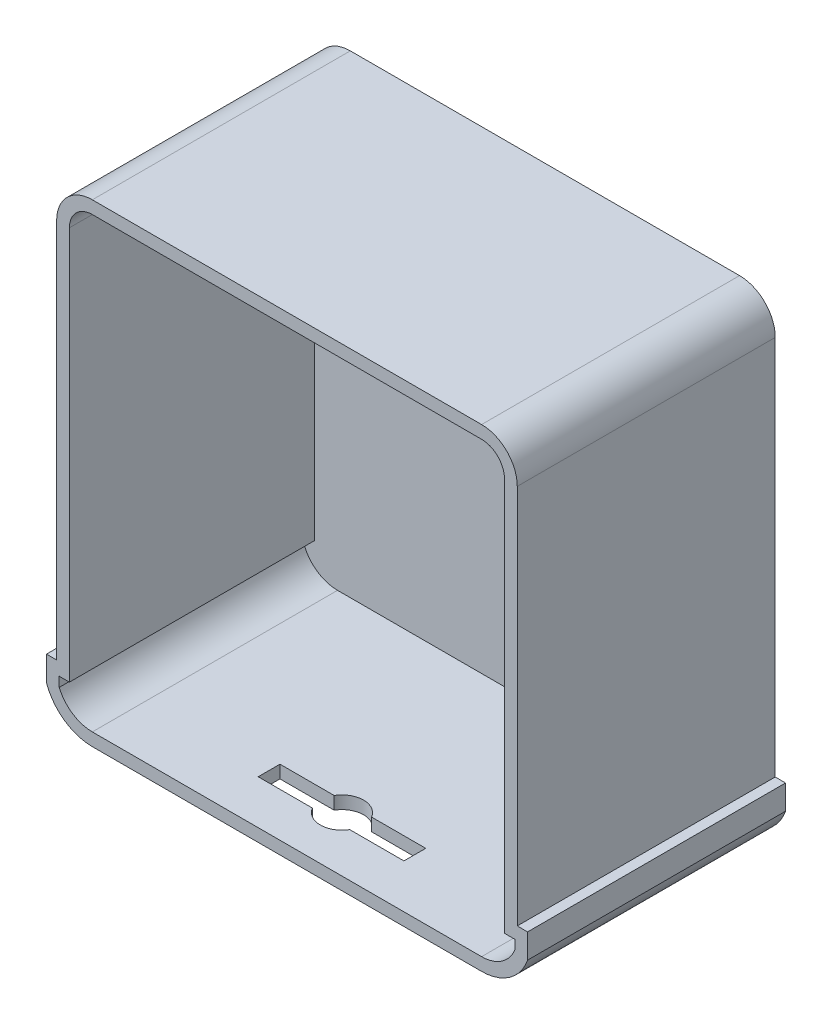
SolidWorks part; units mm, degrees
ref_plane "Front Plane" through (0, 0, 0) normal (0, 0, 1) x (1, 0, 0)
ref_plane "Top Plane" through (0, 0, 0) normal (0, 1, 0) x (1, 0, 0)
ref_plane "Right Plane" through (0, 0, 0) normal (1, 0, 0) x (0, 0, -1)
sketch "Sketch1" plane through (0, 0, 0) normal (0, 0, 1) x (1, 0, 0)
  line L8 (-325.4115, 298.1025) -> (-325.4115, 0)
  line L9 (-325.4115, 0) -> (-333.3926, 0)
  line L10 (-333.3926, 0) -> (-333.3926, -19.3975)
  line L11 (-297.4715, -44.7975) -> (7.3285, -44.7975)
  line L12 (43.3314, -19.1633) -> (43.3314, 0)
  line L13 (43.3314, 0) -> (35.2685, 0)
  line L14 (35.2685, 0) -> (35.2685, 298.1025)
  line L15 (7.3285, 326.0425) -> (-297.4715, 326.0425)
  line L16 (-325.4115, 298.1025) -> (-325.4115, 0)
  line L17 (-325.4115, 0) -> (-333.3926, 0)
  line L18 (-333.3926, 0) -> (-333.3926, -19.3975)
  line L19 (-297.4715, -44.7975) -> (7.3285, -44.7975)
  line L20 (43.3314, -19.1633) -> (43.3314, 0)
  line L21 (43.3314, 0) -> (35.2685, 0)
  line L22 (35.2685, 0) -> (35.2685, 298.1025)
  line L23 (7.3285, 326.0425) -> (-297.4715, 326.0425)
  arc A4 (-333.3926, -19.3975) -> (-297.4715, -44.7975) centre (-297.4715, -6.6975) ccw
  arc A5 (7.3285, -44.7975) -> (43.3314, -19.1633) centre (7.3285, -6.6975) ccw
  arc A6 (35.2685, 298.1025) -> (7.3285, 326.0425) centre (7.3285, 298.1025) ccw
  arc A7 (-297.4715, 326.0425) -> (-325.4115, 298.1025) centre (-297.4715, 298.1025) ccw
  arc A8 (-333.3926, -19.3975) -> (-297.4715, -44.7975) centre (-297.4715, -6.6975) ccw
  arc A9 (7.3285, -44.7975) -> (43.3314, -19.1633) centre (7.3285, -6.6975) ccw
  arc A10 (35.2685, 298.1025) -> (7.3285, 326.0425) centre (7.3285, 298.1025) ccw
  arc A11 (-297.4715, 326.0425) -> (-325.4115, 298.1025) centre (-297.4715, 298.1025) ccw
  dimension "D1" = 0
extrude "Boss-Extrude1" add sketch "Sketch1" along normal blind 10
sketch "Sketch2" plane through (0, 0, 10) normal (0, 0, 1) x (1, 0, 0)
  line L16 (-315.4115, 298.1025) -> (-315.4115, -10)
  line L17 (-315.4115, -10) -> (-323.3926, -10)
  line L18 (-323.3926, -10) -> (-323.3926, -17.547)
  line L19 (-297.4715, -34.7975) -> (7.3285, -34.7975)
  line L20 (33.3314, -17.3491) -> (33.3314, -10)
  line L21 (33.3314, -10) -> (25.2685, -10)
  line L22 (25.2685, -10) -> (25.2685, 298.1025)
  line L23 (7.3285, 316.0425) -> (-297.4715, 316.0425)
  line L24 (-315.4115, 298.1025) -> (-315.4115, -10)
  line L25 (-315.4115, -10) -> (-323.3926, -10)
  line L26 (-323.3926, -10) -> (-323.3926, -17.547)
  line L27 (-297.4715, -34.7975) -> (7.3285, -34.7975)
  line L28 (33.3314, -17.3491) -> (33.3314, -10)
  line L29 (33.3314, -10) -> (25.2685, -10)
  line L30 (25.2685, -10) -> (25.2685, 298.1025)
  line L31 (7.3285, 316.0425) -> (-297.4715, 316.0425)
  line L32 (-325.4115, 298.1025) -> (-325.4115, 0)
  line L33 (-325.4115, 0) -> (-333.3926, 0)
  line L34 (-333.3926, 0) -> (-333.3926, -19.3975)
  line L35 (-297.4715, -44.7975) -> (7.3285, -44.7975)
  line L36 (43.3314, -19.1633) -> (43.3314, 0)
  line L37 (43.3314, 0) -> (35.2685, 0)
  line L38 (35.2685, 0) -> (35.2685, 298.1025)
  line L39 (7.3285, 326.0425) -> (-297.4715, 326.0425)
  line L40 (-325.4115, 298.1025) -> (-325.4115, 0)
  line L41 (-325.4115, 0) -> (-333.3926, 0)
  line L42 (-333.3926, 0) -> (-333.3926, -19.3975)
  line L43 (-297.4715, -44.7975) -> (7.3285, -44.7975)
  line L44 (43.3314, -19.1633) -> (43.3314, 0)
  line L45 (43.3314, 0) -> (35.2685, 0)
  line L46 (35.2685, 0) -> (35.2685, 298.1025)
  line L47 (7.3285, 326.0425) -> (-297.4715, 326.0425)
  arc A8 (-297.4715, 316.0425) -> (-315.4115, 298.1025) centre (-297.4715, 298.1025) ccw
  arc A9 (-323.3926, -17.547) -> (-297.4715, -34.7975) centre (-297.4715, -6.6975) ccw
  arc A10 (7.3285, -34.7975) -> (33.3314, -17.3491) centre (7.3285, -6.6975) ccw
  arc A11 (25.2685, 298.1025) -> (7.3285, 316.0425) centre (7.3285, 298.1025) ccw
  arc A12 (-297.4715, 316.0425) -> (-315.4115, 298.1025) centre (-297.4715, 298.1025) ccw
  arc A13 (-323.3926, -17.547) -> (-297.4715, -34.7975) centre (-297.4715, -6.6975) ccw
  arc A14 (7.3285, -34.7975) -> (33.3314, -17.3491) centre (7.3285, -6.6975) ccw
  arc A15 (25.2685, 298.1025) -> (7.3285, 316.0425) centre (7.3285, 298.1025) ccw
  arc A16 (-297.4715, 326.0425) -> (-325.4115, 298.1025) centre (-297.4715, 298.1025) ccw
  arc A17 (-333.3926, -19.3975) -> (-297.4715, -44.7975) centre (-297.4715, -6.6975) ccw
  arc A18 (7.3285, -44.7975) -> (43.3314, -19.1633) centre (7.3285, -6.6975) ccw
  arc A19 (35.2685, 298.1025) -> (7.3285, 326.0425) centre (7.3285, 298.1025) ccw
  arc A20 (-297.4715, 326.0425) -> (-325.4115, 298.1025) centre (-297.4715, 298.1025) ccw
  arc A21 (-333.3926, -19.3975) -> (-297.4715, -44.7975) centre (-297.4715, -6.6975) ccw
  arc A22 (7.3285, -44.7975) -> (43.3314, -19.1633) centre (7.3285, -6.6975) ccw
  arc A23 (35.2685, 298.1025) -> (7.3285, 326.0425) centre (7.3285, 298.1025) ccw
  dimension "D1" = 10
  dimension "D2" = 0
extrude "Boss-Extrude2" add sketch "Sketch2" along normal blind 192
sketch "Sketch3" plane through (0, -44.7975, 0) normal (0, -1, 0) x (1, 0, 0)
  line L1 (-202.1393, 150.4117) -> (-88.0038, 150.4117)
  line L2 (-202.1393, 150.4117) -> (-202.1393, 167.4708)
  line L3 (-202.1393, 167.4708) -> (-88.0038, 167.4708)
  line L4 (-88.0038, 150.4117) -> (-88.0038, 167.4708)
  line L5 (-202.1393, 150.4117) -> (-88.0038, 167.4708) construction
  line L6 (-202.1393, 167.4708) -> (-88.0038, 150.4117) construction
  circle A0 centre (-145.0715, 158.9412) radius 16.9312
  point P0 (-145.0715, 158.9412)
extrude "Cut-Extrude1" cut sketch "Sketch3" against normal blind 192 contours L3 A0 | L1 A0 L3 | A0 L1 L4 L3 | A0 L3 L2 L1 | L1 A0
